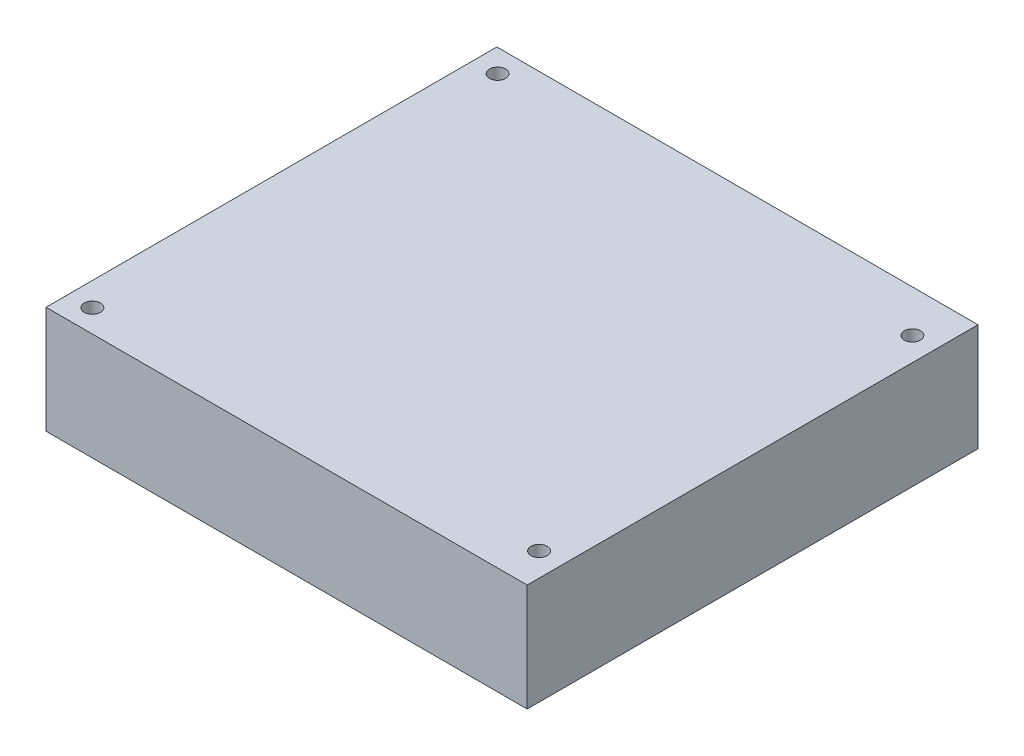
SolidWorks part; units mm, degrees
ref_plane "Front Plane" through (0, 0, 0) normal (0, 0, 1) x (1, 0, 0)
ref_plane "Top Plane" through (0, 0, 0) normal (0, 1, 0) x (1, 0, 0)
ref_plane "Right Plane" through (0, 0, 0) normal (1, 0, 0) x (0, 0, -1)
sketch "Sketch1" plane through (0, 0, 0) normal (0, 1, 0) x (1, 0, 0)
  line L1 (-47.5, -44.505) -> (47.5, -44.505)
  line L2 (-47.5, -44.505) -> (-47.5, 44.505)
  line L3 (-47.5, 44.505) -> (47.5, 44.505)
  line L4 (47.5, -44.505) -> (47.5, 44.505)
  line L5 (-47.5, -44.505) -> (47.5, 44.505) construction
  line L6 (-47.5, 44.505) -> (47.5, -44.505) construction
  circle A0 centre (-42.85, 40) radius 1.6
  circle A1 centre (42.85, 36.2) radius 1.6
  circle A2 centre (-42.85, -40) radius 1.6
  circle A3 centre (42.85, -37.5) radius 1.6
  point P0 (47.5, 44.505)
  point P1 (0, 0)
  point P7 (42.85, 36.2)
  point P8 (42.85, -37.5)
  point P9 (-42.85, 40)
  point P10 (-42.85, -40)
extrude "Boss-Extrude1" add sketch "Sketch1" along normal blind 21.2
